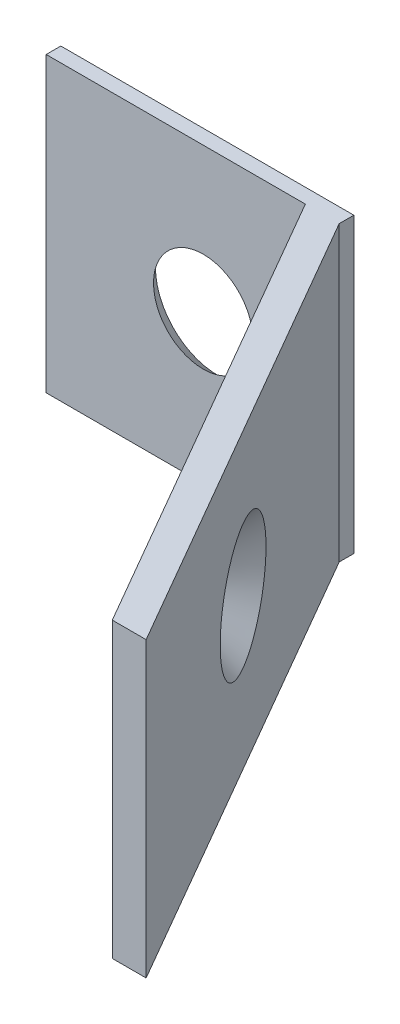
SolidWorks part; units mm, degrees
ref_plane "Front Plane" through (0, 0, 0) normal (0, 0, 1) x (1, 0, 0)
ref_plane "Top Plane" through (0, 0, 0) normal (0, 1, 0) x (1, 0, 0)
ref_plane "Right Plane" through (0, 0, 0) normal (1, 0, 0) x (0, 0, -1)
sketch "Sketch2" plane through (0, 0, 0) normal (0, 0, 1) x (1, 0, 0)
  line L0 (5, 0) -> (5, -10) construction
  line L1 (0, 0) -> (10, 0)
  line L2 (0, 0) -> (0, -10)
  line L3 (0, -10) -> (10, -10)
  line L4 (10, 0) -> (10, -10)
  line L5 (5, -10) -> (0, -5) construction
  line L6 (0, -5) -> (10.1099, -5) construction
  dimension "D1" = 10
  dimension "D2" = 10
extrude "Boss-Extrude1" add sketch "Sketch2" along normal blind 0.5
sketch "Sketch3" plane through (0, -10, 0) normal (0, -1, 0) x (1, 0, 0)
  line L0 (8.8453, 0.5) -> (17.8453, 16.0885)
  line L1 (0, 0.5) -> (10, 0.5) construction
  line L2 (17.8453, 16.0885) -> (19, 16.0885)
  line L3 (19, 16.0885) -> (10, 0.5)
  line L4 (10, 0.5) -> (8.8453, 0.5)
  dimension "D1" = 120
  dimension "D2" = 18
  dimension "D3" = 1
extrude "Boss-Extrude2" add sketch "Sketch3" against normal blind 10
sketch "Sketch6" plane through (0, 0, 0) normal (0, 0, -1) x (-1, 0, 0)
  point P0 (-5.3625, -4.9213)
hole_wizard "CSK for #1 Flat Head Socket Cap Screw1" positions "Sketch6" profile "Sketch7" countersink size "#1" standard "ANSI Inch" end condition through all
sketch "Sketch7" plane through (5.3625, -4.9213, 0) normal (1, 0, 0) x (0, 1, 0)
  line L0 (0, 0) -> (0, 16.0885)
  line L1 (0, 16.0885) -> (1.0287, 16.0885)
  line L2 (1.0287, 16.0885) -> (1.0287, 1.271)
  line L3 (1.0287, 1.271) -> (2.1336, 0)
  line L5 (2.1336, 0) -> (0, 0)
  line L6 (-1.0287, 1.271) -> (-2.1336, 0) construction
  line L11 (0, -6.35) -> (0, 107.95) construction
  dimension "Thru Hole Dia." = 2.0574
  dimension "Thru Hole Depth" = 16.0885
  dimension "Near C'Sink Dia." = 4.2672
  dimension "Near C'Sink Angle" = 82
sketch "Sketch8" plane through (7.2835, 0, -4.2051) normal (0.866, 0, -0.5) x (-0.5, 0, -0.866)
  point P0 (-14.3915, -4.8794)
hole_wizard "CSK for #1 Flat Head Socket Cap Screw2" positions "Sketch8" profile "Sketch9" countersink size "#1" standard "ANSI Inch" end condition through all
sketch "Sketch9" plane through (14.4792, -4.8794, 8.2582) normal (0, 1, 0) x (-0.5, 0, -0.866)
  line L0 (0, 0) -> (0, 16.4545)
  line L1 (0, 16.4545) -> (1.0287, 16.4545)
  line L2 (1.0287, 16.4545) -> (1.0287, 1.271)
  line L3 (1.0287, 1.271) -> (2.1336, 0)
  line L5 (2.1336, 0) -> (0, 0)
  line L6 (-1.0287, 1.271) -> (-2.1336, 0) construction
  line L11 (0, -6.35) -> (0, 107.95) construction
  dimension "Thru Hole Dia." = 2.0574
  dimension "Thru Hole Depth" = 16.4545
  dimension "Near C'Sink Dia." = 4.2672
  dimension "Near C'Sink Angle" = 82
